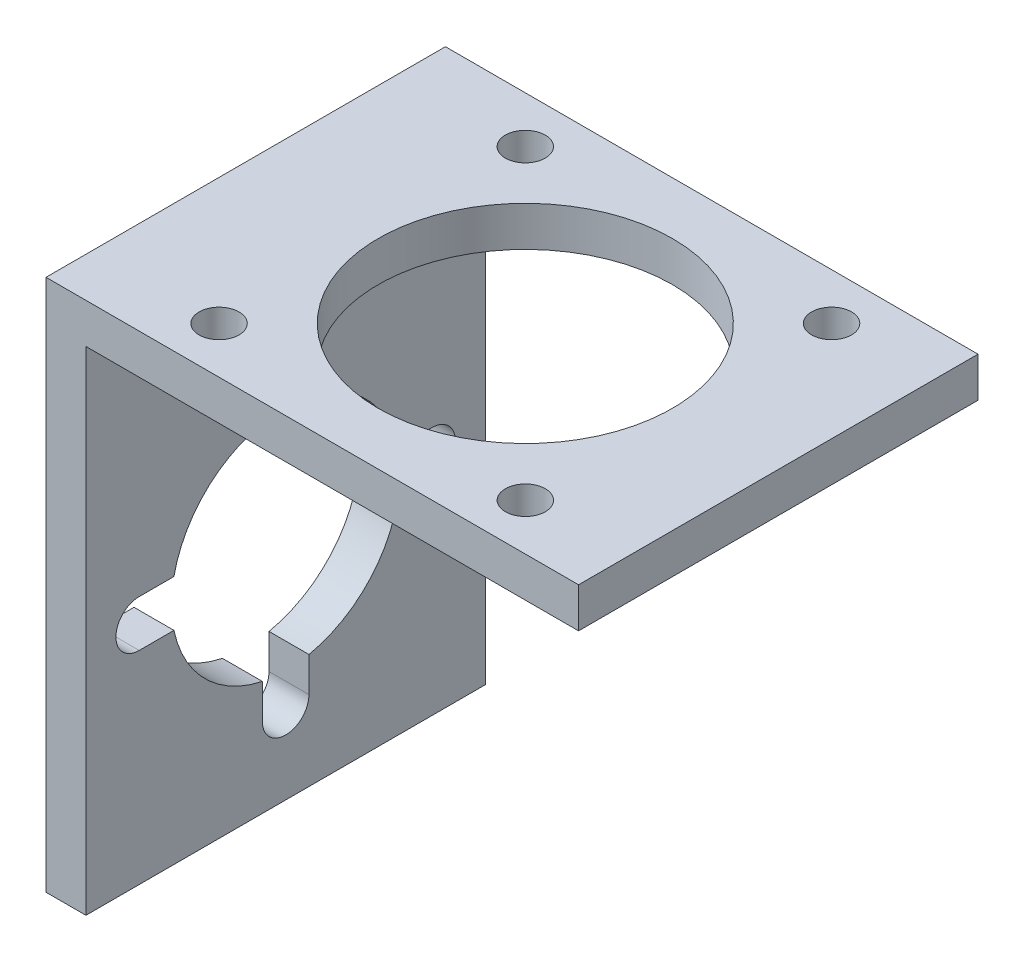
SolidWorks part; units mm, degrees
ref_plane "Front Plane" through (0, 0, 0) normal (0, 0, 1) x (1, 0, 0)
ref_plane "Top Plane" through (0, 0, 0) normal (0, 1, 0) x (1, 0, 0)
ref_plane "Right Plane" through (0, 0, 0) normal (1, 0, 0) x (0, 0, -1)
sketch "Sketch1" plane through (0, 0, 0) normal (0, 0, 1) x (1, 0, 0)
  line L1 (0, 0) -> (40, 0)
  line L2 (0, 0) -> (0, -3)
  line L3 (3, -3) -> (40, -3)
  line L4 (40, 0) -> (40, -3)
  line L6 (0, -3) -> (0, -40)
  line L7 (0, -40) -> (3, -40)
  line L8 (3, -3) -> (3, -40)
  dimension "D1" = 40
  dimension "D2" = 40
  dimension "D3" = 3
  dimension "D4" = 3
extrude "Boss-Extrude1" add sketch "Sketch1" along normal blind 30
sketch "Sketch2" plane through (0, -3, 0) normal (0, -1, 0) x (1, 0, 0)
  line L0 (40, 15) -> (3, 15) construction
  line L1 (40, 30) -> (40, 0) construction
  line L2 (3, 30) -> (3, 0) construction
  circle A0 centre (21, 15) radius 11.05
  circle A1 centre (21, 15) radius 16.265 construction
  circle A2 centre (32.5022, 26.5) radius 1.5
  circle A3 centre (32.5, 3.4978) radius 1.5
  circle A4 centre (9.4978, 3.5) radius 1.5
  circle A5 centre (9.5, 26.5022) radius 1.5
  point P20 (21, 15)
  dimension "D1" = 22.1
  dimension "D2" = 19
  dimension "D3" = 32.53
  dimension "D4" = 3
  dimension "D5" = 11.5
  dimension "D7" = 23.0022
  dimension "D6" = 4
extrude "Cut-Extrude1" cut sketch "Sketch2" against normal through all
sketch "Sketch3" plane through (3, 0, 0) normal (1, 0, 0) x (0, 0, -1)
  line L0 (-15, -40) -> (-15, -12.8414) construction
  line L1 (-30, -40) -> (0, -40) construction
  line L3 (-26, -21.27) -> (-23.3894, -21.27)
  line L4 (-26, -24.77) -> (-23.3894, -24.77)
  line L5 (-16.75, -12.02) -> (-16.75, -14.6306)
  line L6 (-13.25, -12.02) -> (-13.25, -14.6306)
  line L7 (-4, -21.27) -> (-6.6106, -21.27)
  line L8 (-4, -24.77) -> (-6.6106, -24.77)
  line L9 (-16.75, -34.02) -> (-16.75, -31.4094)
  line L10 (-13.25, -34.02) -> (-13.25, -31.4094)
  arc A0 (-23.3894, -24.77) -> (-16.75, -31.4094) centre (-15, -23.02) ccw
  circle A1 centre (-15, -23.02) radius 11 construction
  arc A2 (-16.75, -34.02) -> (-13.25, -34.02) centre (-15, -34.02) ccw
  arc A3 (-26, -21.27) -> (-26, -24.77) centre (-26, -23.02) ccw
  arc A4 (-13.25, -12.02) -> (-16.75, -12.02) centre (-15, -12.02) ccw
  arc A5 (-4, -24.77) -> (-4, -21.27) centre (-4, -23.02) ccw
  arc A6 (-16.75, -14.6306) -> (-23.3894, -21.27) centre (-15, -23.02) ccw
  arc A7 (-6.6106, -21.27) -> (-13.25, -14.6306) centre (-15, -23.02) ccw
  arc A8 (-13.25, -31.4094) -> (-6.6106, -24.77) centre (-15, -23.02) ccw
  point P20 (-15, -23.02)
  dimension "D1" = 17.14
  dimension "D2" = 16.98
  dimension "D3" = 22
  dimension "D4" = 3.5
  dimension "D5" = 4
extrude "Cut-Extrude2" cut sketch "Sketch3" against normal through all
